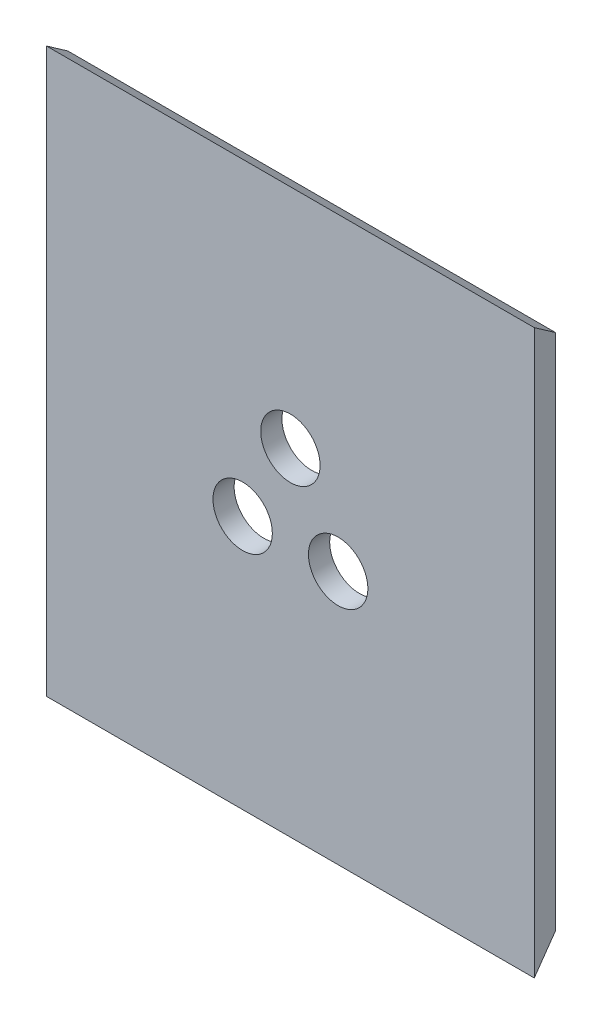
SolidWorks part; units mm, degrees
ref_plane "Front Plane" through (0, 0, 0) normal (0, 0, 1) x (1, 0, 0)
ref_plane "Top Plane" through (0, 0, 0) normal (0, 1, 0) x (1, 0, 0)
ref_plane "Right Plane" through (0, 0, 0) normal (1, 0, 0) x (0, 0, -1)
sketch "Sketch1" plane through (0, 0, 0) normal (0, 0, 1) x (1, 0, 0)
  line L0 (0, 111.7413) -> (0, -115.75) construction
  line L1 (-57.5, 66.4) -> (57.5, 66.4)
  line L2 (-57.5, 66.4) -> (-57.5, -66.4)
  line L3 (-57.5, -66.4) -> (57.5, -66.4)
  line L4 (57.5, 66.4) -> (57.5, -66.4)
  line L5 (-91.698, 0) -> (159.8452, 0) construction
  line L6 (0, 0) -> (-46.1885, -26.667) construction
  circle A0 centre (0, 0) radius 13 construction
  circle A1 centre (0, 13) radius 7
  circle A2 centre (-11.2583, -6.5) radius 7
  circle A3 centre (11.2583, -6.5) radius 7
  dimension "D3" = 26
  dimension "D4" = 14
  dimension "D6" = 14
  dimension "D1" = 132.8
  dimension "D2" = 115
  dimension "D5" = 120
extrude "Boss-Extrude1" add sketch "Sketch1" along normal blind 5
sketch "Sketch2" plane through (57.5, 0, 0) normal (1, 0, 0) x (0, 0, -1)
  line L0 (-5, -66.4) -> (0, -66.4)
  line L1 (0, -66.4) -> (0, 66.4) construction
  line L2 (-5, -66.4) -> (0, -66.4) construction
  line L3 (0, -66.4) -> (0, -59.2593)
  line L4 (0, -59.2593) -> (-5, -66.4)
  dimension "D1" = 35
extrude "Cut-Extrude1" cut sketch "Sketch2" against normal up to next
sketch "Sketch3" plane through (57.5, 0, 0) normal (1, 0, 0) x (0, 0, -1)
  line L0 (-5, 66.4) -> (0, 66.4)
  line L1 (0, 66.4) -> (0, 62.899)
  line L2 (0, -59.2593) -> (0, 66.4) construction
  line L3 (0, 62.899) -> (-5, 66.4)
  dimension "D1" = 35
extrude "Cut-Extrude2" cut sketch "Sketch3" against normal up to next
